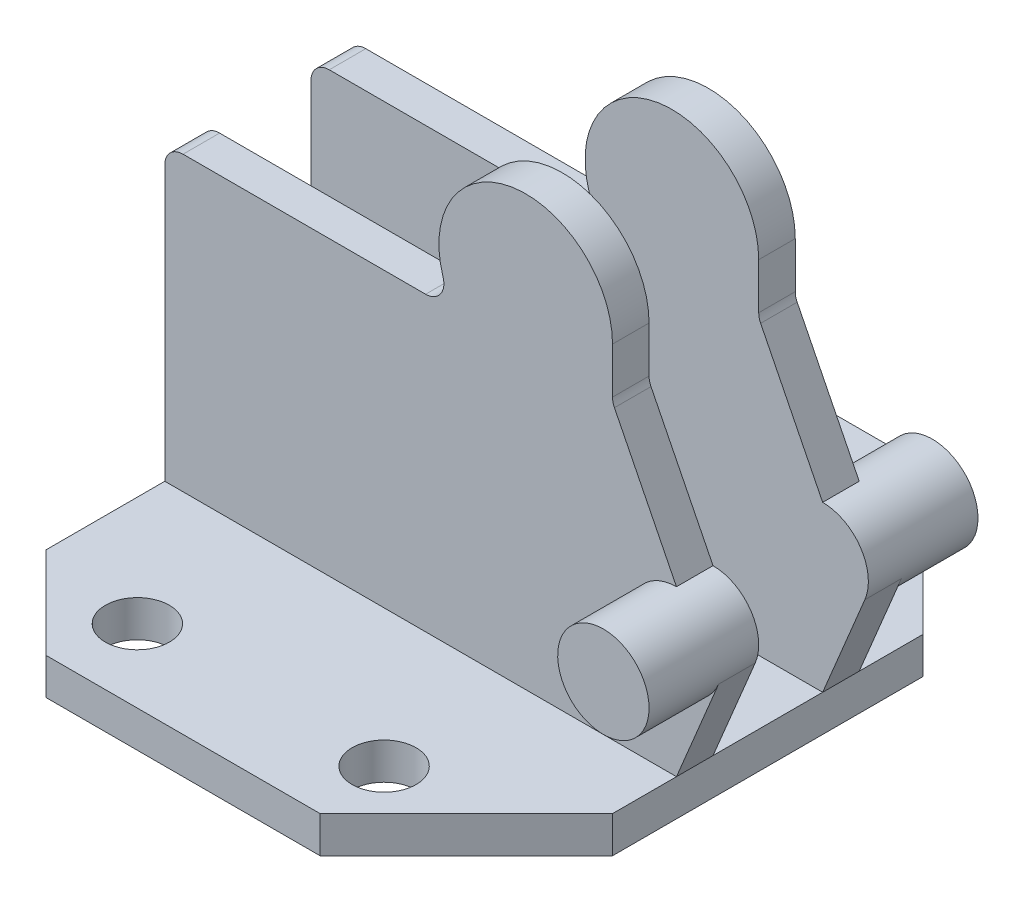
SolidWorks part; units mm, degrees
ref_plane "Front Plane" through (0, 0, 0) normal (0, 0, 1) x (1, 0, 0)
ref_plane "Top Plane" through (0, 0, 0) normal (0, 1, 0) x (1, 0, 0)
ref_plane "Right Plane" through (0, 0, 0) normal (1, 0, 0) x (0, 0, -1)
sketch "Sketch1" plane through (0, 0, 0) normal (0, 1, 0) x (1, 0, 0)
  line L0 (-28, -23) -> (-18, -33)
  line L1 (-18, 33) -> (12, 33)
  line L2 (-28, 23) -> (-28, -23)
  line L3 (-18, -33) -> (12, -33)
  line L4 (28, 17) -> (28, -17)
  line L5 (-23.4098, 27.5902) -> (20.6557, -24.3443) construction
  line L6 (-28, -33) -> (20.6557, 24.3443) construction
  line L7 (0, 0) -> (-81.5535, 0) construction
  line L8 (12, -33) -> (28, -17)
  line L9 (-81.5535, 0) -> (89.0108, 0) construction
  line L10 (12, 33) -> (28, 17)
  line L11 (-18, 33) -> (12, 33)
  line L12 (-28, 23) -> (-18, 33)
  line L13 (12, 33) -> (28, 17)
  circle A0 centre (-16, -25) radius 3.5
  circle A1 centre (11, -25) radius 3.5
  circle A2 centre (11, 25) radius 3.5
  circle A3 centre (-16, 25) radius 3.5
  point P0 (0, 0)
  dimension "D3" = 7
  dimension "D4" = 7
  dimension "D5" = 8
  dimension "D6" = 12
  dimension "D7" = 27
  dimension "D8" = 8
  dimension "D10" = 45
extrude "Boss-Extrude1" add sketch "Sketch1" along normal blind 4 contours L12 L2 L0 L3 L8 L4 L10 L1 A2 A1 A0 A3
ref_plane "Plane1" through (0, 0, 6) normal (0, 0, 1) x (1, 0, 0)
sketch "Sketch2" plane through (0, 0, 6) normal (0, 0, 1) x (1, 0, 0)
  line L0 (-28, 4) -> (-28, 34)
  line L1 (-28, 4) -> (28, 4)
  line L2 (28, 4) -> (32.6154, 15.0769)
  line L3 (-26, 36) -> (0.5455, 36)
  line L6 (21, 41.5) -> (21, 36.4721)
  line L7 (21.2111, 35.5777) -> (28, 22)
  circle A0 centre (28, 17) radius 5
  arc A1 (21, 41.5) -> (2.4507, 38.6087) centre (11.5, 41.5) ccw
  arc A2 (0.5455, 36) -> (2.4507, 38.6087) centre (0.5455, 38) ccw
  arc A3 (21.2111, 35.5777) -> (21, 36.4721) centre (23, 36.4721) cw
  arc A4 (-28, 34) -> (-26, 36) centre (-26, 34) cw
  point P20 (-28, 36)
  dimension "D3" = 10
  dimension "D4" = 39.5
  dimension "D6" = 19
  dimension "D7" = 2
  dimension "D8" = 2
  dimension "D9" = 2
  dimension "D1" = 32
  dimension "D2" = 13
  dimension "D5" = 37.5
extrude "Boss-Extrude2" add sketch "Sketch2" along normal blind 4 contours A4 L0 L1 L2 A0 L7 A3 L6 A1 A2 L3
sketch "Sketch6" plane through (0, 0, 6) normal (0, 0, 1) x (1, 0, 0)
  circle A0 centre (28, 17) radius 5
  dimension "D1" = 10
extrude "Boss-Extrude3" add sketch "Sketch6" along normal blind 12
sketch "Sketch7" plane through (0, 4, 0) normal (0, 1, 0) x (1, 0, 0)
  line L0 (0, 0) -> (109.647, 0) construction
  line L1 (109.647, 0) -> (-73.3356, 0) construction
mirror "Mirror1" about plane through (0, 0, 0) normal (0, 0, 1) of "Boss-Extrude2"
mirror "Mirror2" about plane through (0, 0, 0) normal (0, 0, 1) of "Boss-Extrude3"
